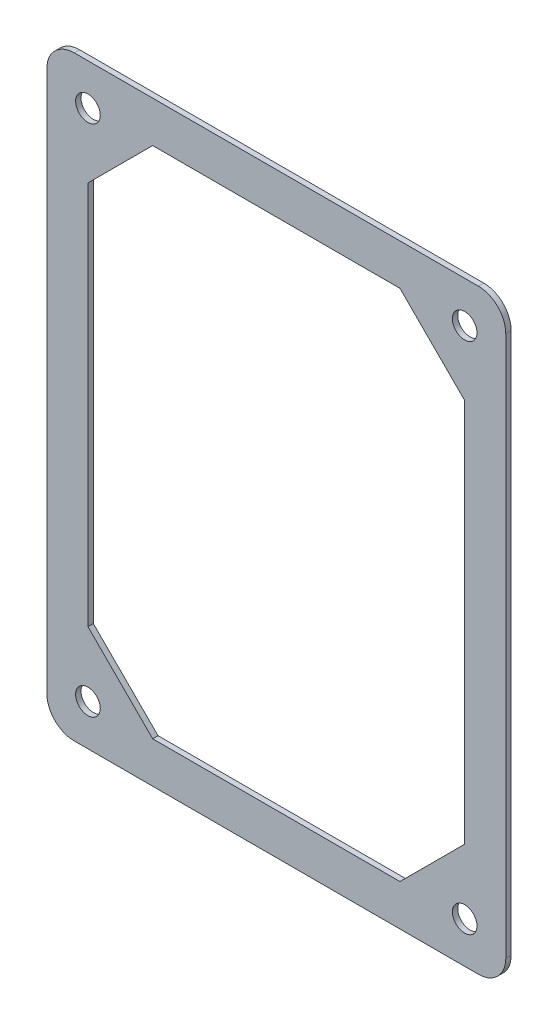
SolidWorks part; units mm, degrees
ref_plane "Front Plane" through (0, 0, 0) normal (0, 0, 1) x (1, 0, 0)
ref_plane "Top Plane" through (0, 0, 0) normal (0, 1, 0) x (1, 0, 0)
ref_plane "Right Plane" through (0, 0, 0) normal (1, 0, 0) x (0, 0, -1)
sketch "Sketch1" plane through (0, 0, 0) normal (0, 0, 1) x (1, 0, 0)
  line L0 (1.27, -104.14) -> (1.27, -3.81) construction
  line L1 (-3.81, 1.27) -> (-78.74, 1.27) construction
  line L2 (-83.82, -3.81) -> (-83.82, -104.14) construction
  line L3 (-78.74, -109.22) -> (-3.81, -109.22) construction
  line L4 (1.27, -104.14) -> (1.27, -3.81)
  line L5 (-3.81, 1.27) -> (-78.74, 1.27)
  line L6 (-83.82, -3.81) -> (-83.82, -104.14)
  line L7 (-78.74, -109.22) -> (-3.81, -109.22)
  line L8 (-76.2, -18.35) -> (-64.2, -6.35)
  line L9 (-64.2, -6.35) -> (-18.35, -6.35)
  line L10 (-76.2, -18.35) -> (-76.2, -89.6)
  line L11 (-64.2, -101.6) -> (-18.35, -101.6)
  line L12 (-6.35, -18.35) -> (-6.35, -89.6)
  line L13 (-18.35, -6.35) -> (-6.35, -18.35)
  line L14 (-18.35, -101.6) -> (-6.35, -89.6)
  line L15 (-76.2, -89.6) -> (-64.2, -101.6)
  circle A0 centre (-76.2, -6.35) radius 2.286 construction
  circle A1 centre (-76.2, -101.6) radius 2.286 construction
  circle A2 centre (-6.35, -101.6) radius 2.286 construction
  circle A3 centre (-6.35, -6.35) radius 2.286 construction
  arc A4 (1.27, -3.81) -> (-3.81, 1.27) centre (-3.81, -3.81) ccw construction
  arc A5 (-78.74, 1.27) -> (-83.82, -3.81) centre (-78.74, -3.81) ccw construction
  arc A6 (-83.82, -104.14) -> (-78.74, -109.22) centre (-78.74, -104.14) ccw construction
  arc A7 (-3.81, -109.22) -> (1.27, -104.14) centre (-3.81, -104.14) ccw construction
  circle A8 centre (-76.2, -6.35) radius 2.286
  circle A9 centre (-76.2, -101.6) radius 2.286
  circle A10 centre (-6.35, -101.6) radius 2.286
  circle A11 centre (-6.35, -6.35) radius 2.286
  arc A12 (1.27, -3.81) -> (-3.81, 1.27) centre (-3.81, -3.81) ccw
  arc A13 (-78.74, 1.27) -> (-83.82, -3.81) centre (-78.74, -3.81) ccw
  arc A14 (-83.82, -104.14) -> (-78.74, -109.22) centre (-78.74, -104.14) ccw
  arc A15 (-3.81, -109.22) -> (1.27, -104.14) centre (-3.81, -104.14) ccw
extrude "Boss-Extrude1" add sketch "Sketch1" along normal blind 1
